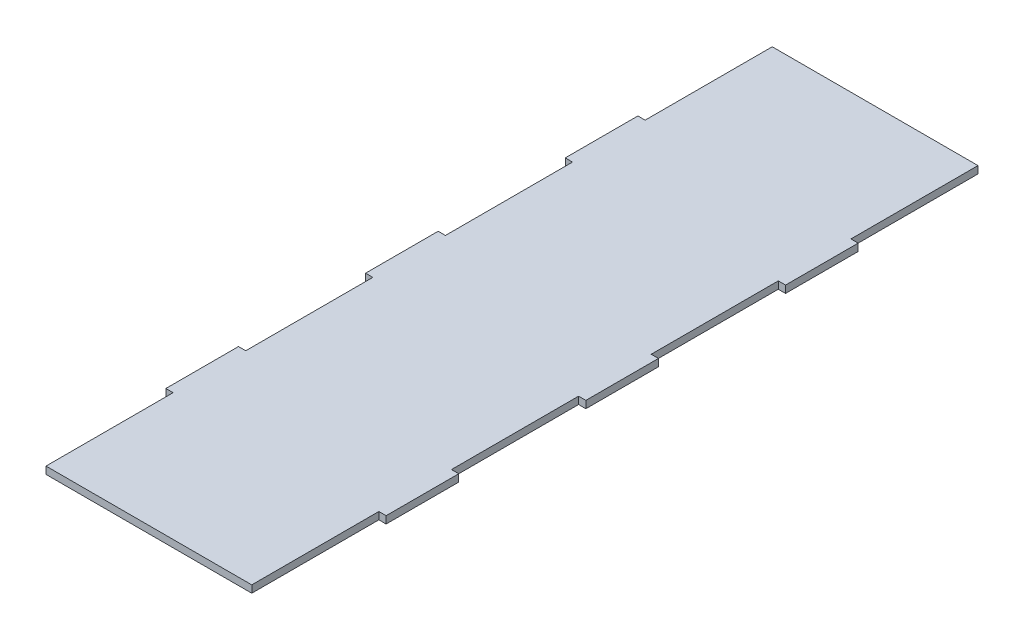
SolidWorks part; units mm, degrees
ref_plane "Alzado" through (0, 0, 0) normal (0, 0, 1) x (1, 0, 0)
ref_plane "Planta" through (0, 0, 0) normal (0, 1, 0) x (1, 0, 0)
ref_plane "Vista lateral" through (0, 0, 0) normal (1, 0, 0) x (0, 0, -1)
sketch "Croquis1" plane through (0, 0, 0) normal (0, 1, 0) x (1, 0, 0)
  line L0 (-45.5, 67.5) -> (-42.5, 67.5)
  line L1 (42.5, -150) -> (-42.5, -150)
  line L2 (42.5, -150) -> (42.5, -97.5)
  line L3 (42.5, 150) -> (-42.5, 150)
  line L4 (-42.5, -150) -> (-42.5, -97.5)
  line L5 (42.5, 97.5) -> (45.5, 97.5)
  line L6 (42.5, 67.5) -> (45.5, 67.5)
  line L7 (-45.5, -97.5) -> (-42.5, -97.5)
  line L8 (-45.5, -97.5) -> (-45.5, -67.5)
  line L9 (-45.5, -67.5) -> (-42.5, -67.5)
  line L10 (45.5, -97.5) -> (45.5, -67.5)
  line L11 (42.5, 15) -> (45.5, 15)
  line L12 (42.5, -15) -> (45.5, -15)
  line L13 (-45.5, 67.5) -> (-45.5, 97.5)
  line L14 (-45.5, 97.5) -> (-42.5, 97.5)
  line L15 (45.5, 67.5) -> (45.5, 97.5)
  line L16 (42.5, -67.5) -> (45.5, -67.5)
  line L17 (42.5, -97.5) -> (45.5, -97.5)
  line L18 (-45.5, -15) -> (-42.5, -15)
  line L19 (-45.5, -15) -> (-45.5, 15)
  line L20 (-45.5, 15) -> (-42.5, 15)
  line L21 (45.5, -15) -> (45.5, 15)
  line L22 (-42.5, -67.5) -> (-42.5, -15)
  line L23 (42.5, -67.5) -> (42.5, -15)
  line L24 (-42.5, 15) -> (-42.5, 67.5)
  line L25 (42.5, 15) -> (42.5, 67.5)
  line L26 (-42.5, 97.5) -> (-42.5, 150)
  line L27 (42.5, 97.5) -> (42.5, 150)
  point P0 (0, 0)
  point P6 (0, -82.5)
  point P11 (0, 82.5)
  point P16 (0, 0)
  dimension "D1" = 85
  dimension "D2" = 300
  dimension "D3" = 91
  dimension "D4" = 30
  dimension "D5" = 91
  dimension "D6" = 30
  dimension "D7" = 91
  dimension "D8" = 30
  dimension "D9" = 82.5
  dimension "D10" = 82.5
extrude "Saliente-Extruir1" add sketch "Croquis1" along normal blind 3
